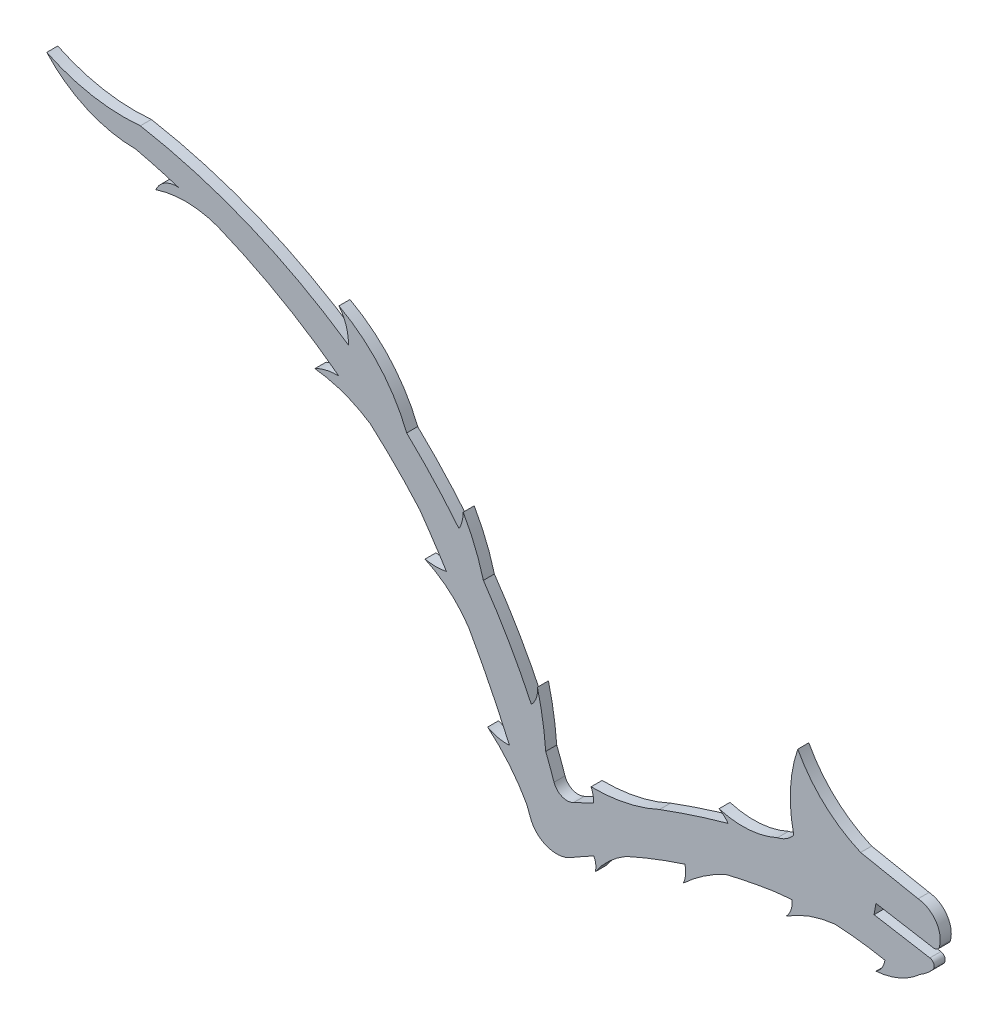
SolidWorks part; units mm, degrees
ref_plane "Front Plane" through (0, 0, 0) normal (0, 0, 1) x (1, 0, 0)
ref_plane "Top Plane" through (0, 0, 0) normal (0, 1, 0) x (1, 0, 0)
ref_plane "Right Plane" through (0, 0, 0) normal (1, 0, 0) x (0, 0, -1)
sketch "Sketch1" plane through (0, 0, 0) normal (0, 0, 1) x (1, 0, 0)
  line L0 (47.3813, -13.0764) -> (55.3439, -14.4324)
  line L1 (53.2202, -9.6006) -> (45.2661, -8.0341)
  line L2 (54.8427, -15.8751) -> (47.1282, -14.5611)
  line L3 (47.1282, -14.5611) -> (47.3813, -13.0764)
  arc A0 (55.3439, -14.4324) -> (56.1639, -13.9063) centre (55.4653, -13.7196) ccw
  arc A1 (56.1639, -13.9063) -> (53.2202, -9.6006) centre (52.8418, -13.0184) ccw
  arc A2 (26.5498, -20.0103) -> (20.7465, -23.9662) centre (36.3875, -40.6768) ccw
  arc A3 (33.7808, -12.0098) -> (36.0188, -10.5865) centre (32.9565, -8.2426) ccw
  arc A4 (26.9202, -13.7196) -> (17.4564, -16.7895) centre (59.9834, -131.768) ccw
  arc A5 (2.8538, -20.832) -> (5.5336, -21.9326) centre (4.6772, -20.205) ccw
  arc A6 (2.8538, -20.832) -> (1.705, -17.7072) centre (-71.7714, -46.4934) ccw
  arc A7 (-25.5984, 17.3262) -> (-54.3705, 29.1994) centre (-67.3191, -42.9766) ccw
  arc A9 (-15.7245, 2.5416) -> (-22.5595, 9.4037) centre (-71.7909, -46.4686) ccw
  arc A10 (-0.4127, -26.7011) -> (-0.9065, -25.3754) centre (-118.6569, -69.9849) ccw
  arc A11 (-0.4127, -26.7011) -> (5.1683, -28.6968) centre (3.2087, -25.3754) ccw
  arc A12 (33.1074, -18.7066) -> (26.5498, -20.0103) centre (45.1613, -96.4798) ccw
  arc A13 (48.6222, -19.2605) -> (41.7229, -18.3962) centre (39.1554, -66.8624) ccw
  arc A14 (53.4699, -18.5447) -> (55.2611, -17.069) centre (50.0695, -12.5925) ccw
  arc A15 (55.2611, -17.069) -> (54.8427, -15.8751) centre (54.7213, -16.5879) ccw
  arc A16 (53.4699, -18.5447) -> (47.3813, -21.1994) centre (46.5739, -11.0381) cw
  arc A17 (47.3813, -21.1994) -> (48.6222, -19.2605) centre (45.9036, -18.8871) ccw
  arc A18 (41.7229, -18.3962) -> (34.9515, -20.832) centre (43.372, -33.6106) ccw
  arc A19 (34.9515, -20.832) -> (35.7628, -18.447) centre (32.9132, -18.8083) ccw
  arc A20 (35.7628, -18.447) -> (33.1074, -18.7066) centre (39.1554, -66.8624) ccw
  arc A21 (45.2661, -8.0341) -> (36.5742, 0) centre (52.396, 8.3983) cw
  arc A22 (36.5742, 0) -> (36.0188, -10.5865) centre (54.9156, -6.2701) ccw
  arc A23 (20.7465, -23.9662) -> (20.9557, -21.5928) centre (17.4564, -22.4803) ccw
  arc A24 (12.8684, -24.7083) -> (8.5626, -28.6968) centre (19.29, -35.9592) ccw
  arc A25 (8.5626, -28.6968) -> (8.3498, -26.9177) centre (6.2693, -28.0688) ccw
  arc A26 (20.9557, -21.5928) -> (12.8684, -24.7083) centre (45.1613, -96.4798) ccw
  arc A27 (8.3498, -26.9177) -> (5.1683, -28.6968) centre (45.1613, -96.4798) ccw
  arc A28 (33.7808, -12.0098) -> (25.67, -12.5925) centre (28.9516, -1.5297) cw
  arc A29 (25.67, -12.5925) -> (26.9202, -13.7196) centre (24.1088, -15.5811) cw
  arc A30 (17.4564, -16.7895) -> (7.9807, -18.8083) centre (8.2918, 2.9796) cw
  arc A31 (7.9807, -18.8083) -> (8.3498, -20.5809) centre (3.7542, -20.6131) cw
  arc A32 (8.3498, -20.5809) -> (5.5336, -21.9326) centre (59.9834, -131.768) ccw
  arc A33 (-0.9065, -25.3754) -> (-6.3291, -18.8083) centre (-21.1143, -36.5392) ccw
  arc A34 (-6.3291, -18.8083) -> (-3.3124, -19.4794) centre (-3.7248, -14.2176) ccw
  arc A35 (-8.916, -8.2426) -> (-14.995, -3.0209) centre (-21.0295, -16.1955) ccw
  arc A36 (-14.995, -3.0209) -> (-12.022, -3.0209) centre (-13.5085, 4.0673) ccw
  arc A37 (-22.5595, 9.4037) -> (-30.2226, 12.1876) centre (-32.1596, -5.0831) ccw
  arc A38 (-30.2226, 12.1876) -> (-26.8972, 12.9451) centre (-27.1925, 6.564) cw
  arc A39 (-43.7032, 22.499) -> (-52.2309, 22.6158) centre (-48.1356, 10.2517) ccw
  arc A40 (-52.2309, 22.6158) -> (-49.1011, 24.4582) centre (-49.3879, 21.3659) cw
  arc A41 (-49.1011, 24.4582) -> (-55.0099, 26.0838) centre (-71.7909, -46.4686) ccw
  arc A42 (-3.3124, -19.4794) -> (-8.916, -8.2426) centre (-118.6569, -69.9849) ccw
  arc A43 (-12.022, -3.0209) -> (-15.7245, 2.5416) centre (-118.6569, -69.9849) ccw
  arc A44 (-26.8972, 12.9451) -> (-43.7032, 22.499) centre (-71.7909, -46.4686) ccw
  arc A45 (1.705, -17.7072) -> (0.5603, -10.5865) centre (-40.6456, -20.8627) ccw
  arc A46 (0.5603, -10.5865) -> (-0.2821, -13.0764) centre (-2.5247, -10.9302) cw
  arc A47 (-0.2821, -13.0764) -> (-6.9201, -1.5297) centre (-71.7714, -46.4934) ccw
  arc A48 (-6.9201, -1.5297) -> (-9.7107, 5.244) centre (-33.7708, -8.6299) ccw
  arc A49 (-9.7107, 5.244) -> (-10.291, 2.9796) centre (-14.3944, 5.2377) cw
  arc A50 (-10.291, 2.9796) -> (-17.5288, 10.8229) centre (-71.7714, -46.4934) ccw
  arc A51 (-17.5288, 10.8229) -> (-26.8972, 21.3659) centre (-36.7112, 3.2114) ccw
  arc A52 (-26.8972, 21.3659) -> (-25.5984, 17.3262) centre (-31.7273, 17.5844) cw
  arc A53 (-54.3705, 29.1994) -> (-67.3191, 31.5224) centre (-56.6722, 53.6193) cw
  arc A54 (-67.3191, 31.5224) -> (-55.0099, 26.0838) centre (-54.9534, 42.8606) ccw
extrude "Boss-Extrude1" add sketch "Sketch1" along normal blind 1.524
